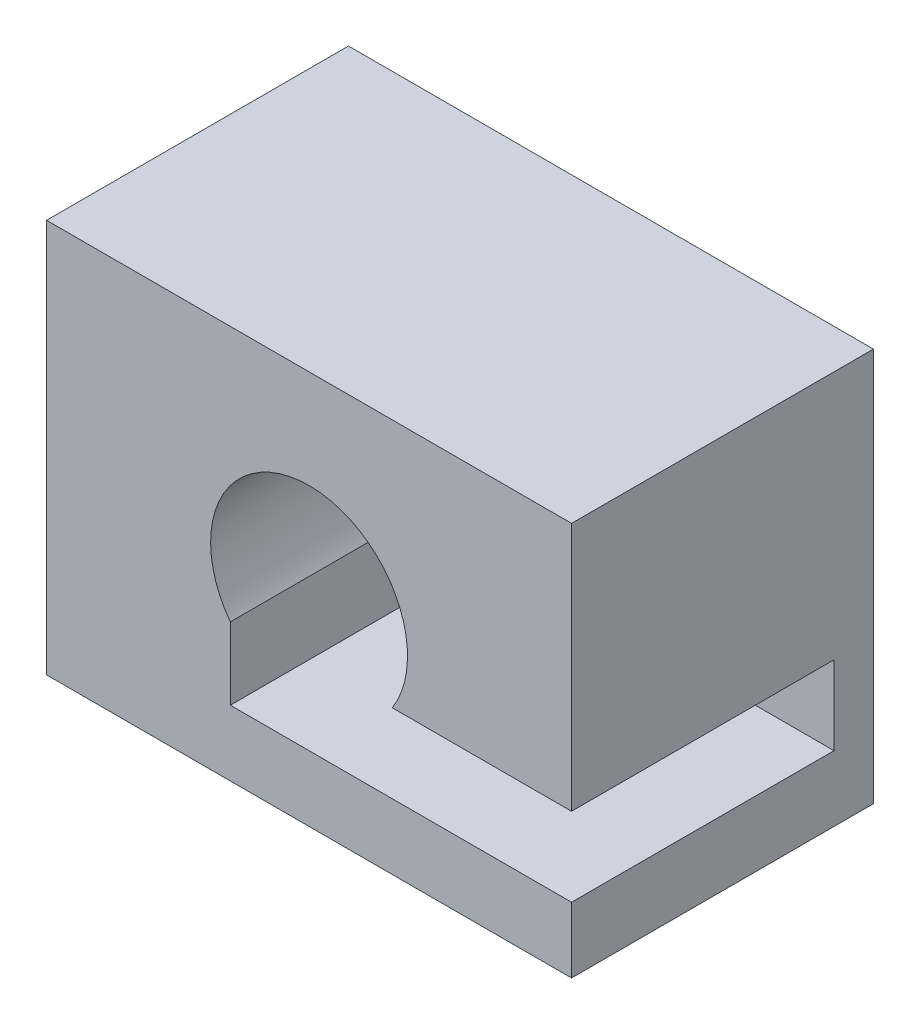
SolidWorks part; units mm, degrees
ref_plane "Front Plane" through (0, 0, 0) normal (0, 0, 1) x (1, 0, 0)
ref_plane "Top Plane" through (0, 0, 0) normal (0, 1, 0) x (1, 0, 0)
ref_plane "Right Plane" through (0, 0, 0) normal (1, 0, 0) x (0, 0, -1)
sketch "Sketch1" plane through (0, 0, 0) normal (0, 0, 1) x (1, 0, 0)
  line L2 (-20, 15) -> (20, 15)
  line L3 (-20, 15) -> (-20, -15)
  line L4 (-20, -15) -> (20, -15)
  line L5 (20, 15) -> (20, -15)
  point P0 (0, 15)
  point P5 (20, 0)
  dimension "D1" = 40
  dimension "D2" = 30
extrude "Boss-Extrude1" add sketch "Sketch1" along normal blind 23 contours L2 L5 L4 L3
sketch "Sketch3" plane through (0, 0, 23) normal (0, 0, 1) x (1, 0, 0)
  circle A0 centre (0, 0) radius 6.1
extrude "Cut-Extrude1" cut sketch "Sketch3" against normal through all
sketch "Sketch4" plane through (0, 0, 23) normal (0, 0, 1) x (1, 0, 0)
  line L0 (20, 15) -> (20, -15) construction
  line L1 (-6, -4) -> (20, -4)
  line L2 (-6, -4) -> (-6, -10)
  line L3 (-6, -10) -> (20, -10)
  line L4 (20, -4) -> (20, -10)
  circle A0 centre (0, 0) radius 7.5
  circle M4 centre (0, 0) radius 6.1
  line M7 (20, -15) -> (20, 15)
  dimension "D1" = 15
  dimension "D2" = 10
  dimension "D3" = 6
  dimension "D4" = 6
extrude "Cut-Extrude2" cut sketch "Sketch4" against normal blind 20 contours L2 A0 L1 M4 | L1 A0 L2 M4 | A0 L2 L3 L1 M7
